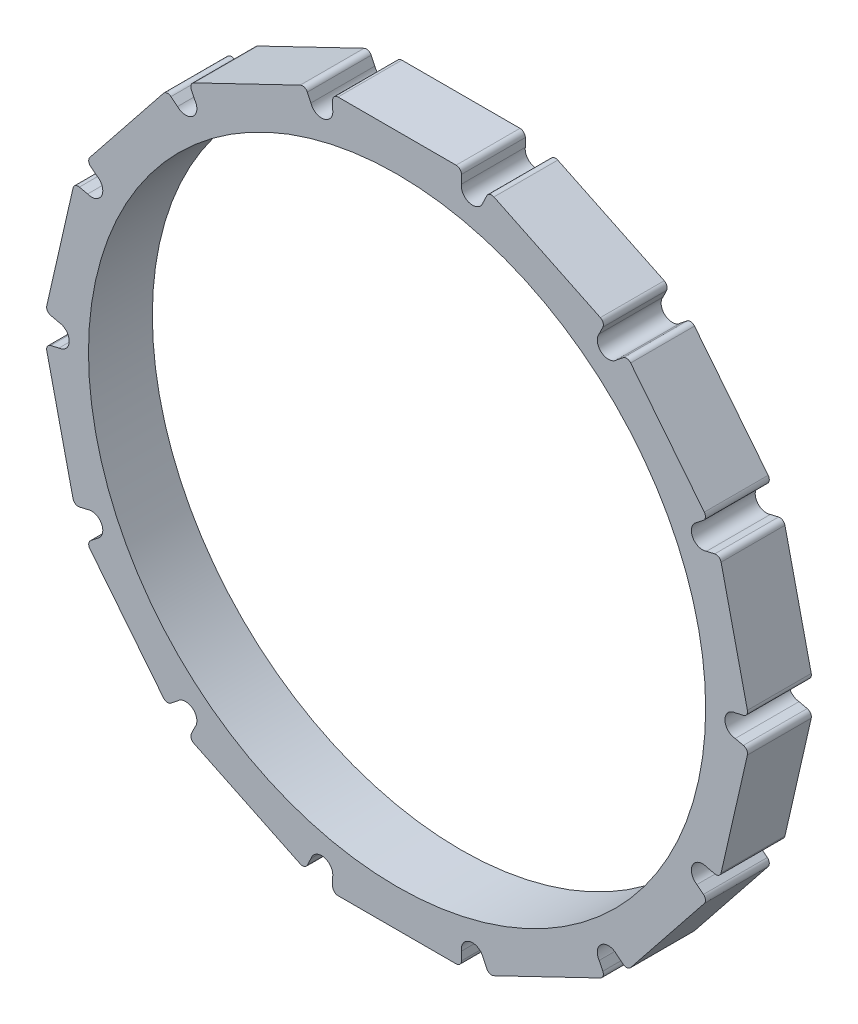
SolidWorks part; units mm, degrees
ref_plane "正面" through (0, 0, 0) normal (0, 0, 1) x (1, 0, 0)
ref_plane "平面" through (0, 0, 0) normal (0, 1, 0) x (1, 0, 0)
ref_plane "右側面" through (0, 0, 0) normal (1, 0, 0) x (0, 0, -1)
sketch "ｽｹｯﾁ1" plane through (0, 0, 0) normal (0, 0, 1) x (1, 0, 0)
  circle A0 centre (0, 0) radius 34.5
  dimension "D1" = 69
extrude "ﾎﾞｽ - 押し出し1" add sketch "ｽｹｯﾁ1" along normal blind 4
sketch "ｽｹｯﾁ2" plane through (0, 0, 4) normal (0, 0, 1) x (1, 0, 0)
  circle A0 centre (0, 0) radius 31.5
  circle A1 centre (0, 0) radius 34.5 construction
  dimension "D1" = 3
extrude "ﾎﾞｽ - 押し出し2" add sketch "ｽｹｯﾁ2" along normal blind 3
sketch "ｽｹｯﾁ3" plane through (0, 0, 4) normal (0, 0, 1) x (1, 0, 0)
  line L1 (-6.05, 30.5) -> (6.05, 30.5)
  line L2 (-6.05, 30.5) -> (-6.05, 32.5)
  line L3 (-6.05, 32.5) -> (6.05, 32.5)
  line L4 (6.05, 30.5) -> (6.05, 32.5)
  line L5 (-6.05, 30.5) -> (6.05, 32.5) construction
  line L6 (-6.05, 32.5) -> (6.05, 30.5) construction
  circle A0 centre (0, 0) radius 31.5 construction
  point P0 (0, 31.5)
  dimension "D1" = 12.1
  dimension "D2" = 1
extrude "ﾎﾞｽ - 押し出し3" add sketch "ｽｹｯﾁ3" along normal blind 3
pattern_circular "円形ﾊﾟﾀｰﾝ1" count 14 over 360 about axis through (0, 0, 0) along (0, 0, 1) of "ﾎﾞｽ - 押し出し3"
sketch "ｽｹｯﾁ5" plane through (0, 0, 7) normal (0, 0, 1) x (1, 0, 0)
  line L0 (-7.0895, 31.0613) -> (0, 0) construction
  circle A0 centre (-7.0895, 31.0613) radius 1.05
  dimension "D1" = 2.1
extrude "ｶｯﾄ - 押し出し1" cut sketch "ｽｹｯﾁ5" against normal blind 3
pattern_circular "円形ﾊﾟﾀｰﾝ2" count 14 over 360 about axis through (0, 0, 0) along (0, 0, 1) of "ｶｯﾄ - 押し出し1"
sketch "ｽｹｯﾁ6" plane through (0, 0, 7) normal (0, 0, 1) x (1, 0, 0)
  circle A0 centre (0, 0) radius 4.5
  dimension "D1" = 9
extrude "ｶｯﾄ - 押し出し2" cut sketch "ｽｹｯﾁ6" against normal through all
sketch "ｽｹｯﾁ7" plane through (0, 0, 7) normal (0, 0, 1) x (1, 0, 0)
  circle A0 centre (0, 0) radius 10.5
  circle A1 centre (0, 0) radius 29
  circle A2 centre (0, 0) radius 4.5 construction
  dimension "D1" = 58
  dimension "D2" = 6
extrude "ｶｯﾄ - 押し出し3" cut sketch "ｽｹｯﾁ7" against normal through all and the other way through all
sketch "ｽｹｯﾁ8" plane through (0, 0, 7) normal (0, 0, 1) x (1, 0, 0)
  line L0 (-10.2329, 2.3534) -> (-4.1739, 28.6981)
  line L1 (0, 29) -> (-4.4863, 9.4933)
  line L2 (0, 0) -> (0, 29) construction
  circle A0 centre (0, 0) radius 10.5 construction
  circle A1 centre (0, 0) radius 29 construction
  arc A2 (0, 29) -> (-4.1739, 28.6981) centre (0, 0) ccw
  arc A3 (-4.4863, 9.4933) -> (-10.2329, 2.3534) centre (0, 0) ccw
  dimension "D1" = 4
extrude "ﾎﾞｽ - 押し出し4" add sketch "ｽｹｯﾁ8" against normal up to surface (7 mm away) up to face at (4.5, 0, 0)
pattern_circular "円形ﾊﾟﾀｰﾝ3" count 6 over 360 about axis through (0, 0, 0) along (0, 0, 1) of "ﾎﾞｽ - 押し出し4"
mirror "ﾐﾗｰ1" about plane through (0, 0, 0) normal (1, 0, 0) of "円形ﾊﾟﾀｰﾝ3", "ﾎﾞｽ - 押し出し4"
fillet "ﾌｨﾚｯﾄ1" radius 0.5 2 edges at (-33.0314, -1.3336, 5.5) (-30.3389, -13.1302, 5.5)
fillet "ﾌｨﾚｯﾄ2" radius 0.5 26 edges at (-8.6504, -31.9065, 5.5) (-6.05, -32.5, 5.5) (6.05, -32.5, 5.5) (8.6504, -31.9065, 5.5) (19.5521, -26.6565, 5.5) (21.6374, -24.9935, 5.5) (29.1816, -15.5333, 5.5) (30.3389, -13.1302, 5.5) (33.0314, -1.3336, 5.5) (33.0314, 1.3336, 5.5) (30.3389, 13.1302, 5.5) (29.1816, 15.5333, 5.5) (21.6374, 24.9935, 5.5) (19.5521, 26.6565, 5.5) (8.6504, 31.9065, 5.5) (6.05, 32.5, 5.5) (-6.05, 32.5, 5.5) (-8.6504, 31.9065, 5.5) (-19.5521, 26.6565, 5.5) (-21.6374, 24.9935, 5.5) (-29.1816, 15.5333, 5.5) (-30.3389, 13.1302, 5.5) (-33.0314, 1.3336, 5.5) (-19.5521, -26.6565, 5.5) (-21.6374, -24.9935, 5.5) (-29.1816, -15.5333, 5.5)
sketch "ｽｹｯﾁ9" plane through (0, 0, 0) normal (0, 0, -1) x (-1, 0, 0)
  circle A0 centre (0, 0) radius 34.5
extrude "ｶｯﾄ - 押し出し4" cut sketch "ｽｹｯﾁ9" against normal blind 4
sketch "ｽｹｯﾁ10" plane through (0, 0, 7) normal (0, 0, 1) x (1, 0, 0)
  circle A0 centre (0, 0) radius 29
extrude "ｶｯﾄ - 押し出し5" cut sketch "ｽｹｯﾁ10" against normal through all
sketch "ｽｹｯﾁ11" plane through (0, 0, 7) normal (0, 0, 1) x (1, 0, 0)
  line L42 (-19.1016, -26.8734) -> (-9.1008, -31.6895)
  line L43 (-8.4334, -31.456) -> (-8.0903, -30.7434)
  line L44 (-6.05, -31.2091) -> (-6.05, -32)
  line L45 (-5.55, -32.5) -> (5.55, -32.5)
  line L46 (6.05, -32) -> (6.05, -31.2091)
  line L47 (8.0903, -30.7434) -> (8.4334, -31.456)
  line L48 (9.1008, -31.6895) -> (19.1016, -26.8734)
  line L49 (19.3351, -26.206) -> (18.992, -25.4935)
  line L50 (20.6282, -24.1887) -> (21.2465, -24.6818)
  line L51 (21.9492, -24.6026) -> (28.8699, -15.9243)
  line L52 (28.7907, -15.2216) -> (28.1724, -14.7285)
  line L53 (29.0804, -12.843) -> (29.8514, -13.019)
  line L54 (30.4502, -12.6428) -> (32.9201, -1.8211)
  line L55 (32.5439, -1.2224) -> (31.7729, -1.0464)
  line L56 (31.7729, 1.0464) -> (32.5439, 1.2224)
  line L57 (32.9201, 1.8211) -> (30.4502, 12.6428)
  line L58 (29.8514, 13.019) -> (29.0804, 12.843)
  line L59 (28.1724, 14.7285) -> (28.7907, 15.2216)
  line L60 (28.8699, 15.9243) -> (21.9492, 24.6026)
  line L61 (21.2465, 24.6818) -> (20.6282, 24.1887)
  line L62 (18.992, 25.4935) -> (19.3351, 26.206)
  line L63 (19.1016, 26.8734) -> (9.1008, 31.6895)
  line L64 (8.4334, 31.456) -> (8.0903, 30.7434)
  line L65 (6.05, 31.2091) -> (6.05, 32)
  line L66 (5.55, 32.5) -> (-5.55, 32.5)
  line L67 (-6.05, 32) -> (-6.05, 31.2091)
  line L68 (-8.0903, 30.7434) -> (-8.4334, 31.456)
  line L69 (-9.1008, 31.6895) -> (-19.1016, 26.8734)
  line L70 (-19.3351, 26.206) -> (-18.992, 25.4935)
  line L71 (-20.6282, 24.1887) -> (-21.2465, 24.6818)
  line L72 (-21.9492, 24.6026) -> (-28.8699, 15.9243)
  line L73 (-28.7907, 15.2216) -> (-28.1724, 14.7285)
  line L74 (-29.0804, 12.843) -> (-29.8514, 13.019)
  line L75 (-30.4502, 12.6428) -> (-32.9201, 1.8211)
  line L76 (-32.5439, 1.2224) -> (-31.7729, 1.0464)
  line L77 (-31.7729, -1.0464) -> (-32.5439, -1.2224)
  line L78 (-32.9201, -1.8211) -> (-30.4502, -12.6428)
  line L79 (-29.8514, -13.019) -> (-29.0804, -12.843)
  line L80 (-28.1724, -14.7285) -> (-28.7907, -15.2216)
  line L81 (-28.8699, -15.9243) -> (-21.9492, -24.6026)
  line L82 (-21.2465, -24.6818) -> (-20.6282, -24.1887)
  line L83 (-18.992, -25.4935) -> (-19.3351, -26.206)
  line L84 (-19.1016, -26.8734) -> (-9.1008, -31.6895)
  line L85 (-8.4334, -31.456) -> (-8.0903, -30.7434)
  line L86 (-6.05, -31.2091) -> (-6.05, -32)
  line L87 (-5.55, -32.5) -> (5.55, -32.5)
  line L88 (6.05, -32) -> (6.05, -31.2091)
  line L89 (8.0903, -30.7434) -> (8.4334, -31.456)
  line L90 (9.1008, -31.6895) -> (19.1016, -26.8734)
  line L91 (19.3351, -26.206) -> (18.992, -25.4935)
  line L92 (20.6282, -24.1887) -> (21.2465, -24.6818)
  line L93 (21.9492, -24.6026) -> (28.8699, -15.9243)
  line L94 (28.7907, -15.2216) -> (28.1724, -14.7285)
  line L95 (29.0804, -12.843) -> (29.8514, -13.019)
  line L96 (30.4502, -12.6428) -> (32.9201, -1.8211)
  line L97 (32.5439, -1.2224) -> (31.7729, -1.0464)
  line L98 (31.7729, 1.0464) -> (32.5439, 1.2224)
  line L99 (32.9201, 1.8211) -> (30.4502, 12.6428)
  line L100 (29.8514, 13.019) -> (29.0804, 12.843)
  line L101 (28.1724, 14.7285) -> (28.7907, 15.2216)
  line L102 (28.8699, 15.9243) -> (21.9492, 24.6026)
  line L103 (21.2465, 24.6818) -> (20.6282, 24.1887)
  line L104 (18.992, 25.4935) -> (19.3351, 26.206)
  line L105 (19.1016, 26.8734) -> (9.1008, 31.6895)
  line L106 (8.4334, 31.456) -> (8.0903, 30.7434)
  line L107 (6.05, 31.2091) -> (6.05, 32)
  line L108 (5.55, 32.5) -> (-5.55, 32.5)
  line L109 (-6.05, 32) -> (-6.05, 31.2091)
  line L110 (-8.0903, 30.7434) -> (-8.4334, 31.456)
  line L111 (-9.1008, 31.6895) -> (-19.1016, 26.8734)
  line L112 (-19.3351, 26.206) -> (-18.992, 25.4935)
  line L113 (-20.6282, 24.1887) -> (-21.2465, 24.6818)
  line L114 (-21.9492, 24.6026) -> (-28.8699, 15.9243)
  line L115 (-28.7907, 15.2216) -> (-28.1724, 14.7285)
  line L116 (-29.0804, 12.843) -> (-29.8514, 13.019)
  line L117 (-30.4502, 12.6428) -> (-32.9201, 1.8211)
  line L118 (-32.5439, 1.2224) -> (-31.7729, 1.0464)
  line L119 (-31.7729, -1.0464) -> (-32.5439, -1.2224)
  line L120 (-32.9201, -1.8211) -> (-30.4502, -12.6428)
  line L121 (-29.8514, -13.019) -> (-29.0804, -12.843)
  line L122 (-28.1724, -14.7285) -> (-28.7907, -15.2216)
  line L123 (-28.8699, -15.9243) -> (-21.9492, -24.6026)
  line L124 (-21.2465, -24.6818) -> (-20.6282, -24.1887)
  line L125 (-18.992, -25.4935) -> (-19.3351, -26.206)
  circle A1 centre (0, 0) radius 29
  circle A2 centre (0, 0) radius 29
  arc A44 (-9.1008, -31.6895) -> (-8.4334, -31.456) centre (-8.8839, -31.2391) ccw
  arc A45 (-6.05, -31.2091) -> (-8.0903, -30.7434) centre (-7.0895, -31.0613) ccw
  arc A46 (-6.05, -32) -> (-5.55, -32.5) centre (-5.55, -32) ccw
  arc A47 (5.55, -32.5) -> (6.05, -32) centre (5.55, -32) ccw
  arc A48 (8.0903, -30.7434) -> (6.05, -31.2091) centre (7.0895, -31.0613) ccw
  arc A49 (8.4334, -31.456) -> (9.1008, -31.6895) centre (8.8839, -31.2391) ccw
  arc A50 (19.1016, -26.8734) -> (19.3351, -26.206) centre (18.8847, -26.4229) ccw
  arc A51 (20.6282, -24.1887) -> (18.992, -25.4935) centre (19.8645, -24.9093) ccw
  arc A52 (21.2465, -24.6818) -> (21.9492, -24.6026) centre (21.5582, -24.2908) ccw
  arc A53 (28.8699, -15.9243) -> (28.7907, -15.2216) centre (28.479, -15.6125) ccw
  arc A54 (29.0804, -12.843) -> (28.1724, -14.7285) centre (28.705, -13.8236) ccw
  arc A55 (29.8514, -13.019) -> (30.4502, -12.6428) centre (29.9627, -12.5315) ccw
  arc A56 (32.9201, -1.8211) -> (32.5439, -1.2224) centre (32.4327, -1.7098) ccw
  arc A57 (31.7729, 1.0464) -> (31.7729, -1.0464) centre (31.8601, 0) ccw
  arc A58 (32.5439, 1.2224) -> (32.9201, 1.8211) centre (32.4327, 1.7098) ccw
  arc A59 (30.4502, 12.6428) -> (29.8514, 13.019) centre (29.9627, 12.5315) ccw
  arc A60 (28.1724, 14.7285) -> (29.0804, 12.843) centre (28.705, 13.8236) ccw
  arc A61 (28.7907, 15.2216) -> (28.8699, 15.9243) centre (28.479, 15.6125) ccw
  arc A62 (21.9492, 24.6026) -> (21.2465, 24.6818) centre (21.5582, 24.2908) ccw
  arc A63 (18.992, 25.4935) -> (20.6282, 24.1887) centre (19.8645, 24.9093) ccw
  arc A64 (19.3351, 26.206) -> (19.1016, 26.8734) centre (18.8847, 26.4229) ccw
  arc A65 (9.1008, 31.6895) -> (8.4334, 31.456) centre (8.8839, 31.2391) ccw
  arc A66 (6.05, 31.2091) -> (8.0903, 30.7434) centre (7.0895, 31.0613) ccw
  arc A67 (6.05, 32) -> (5.55, 32.5) centre (5.55, 32) ccw
  arc A68 (-5.55, 32.5) -> (-6.05, 32) centre (-5.55, 32) ccw
  arc A69 (-8.0903, 30.7434) -> (-6.05, 31.2091) centre (-7.0895, 31.0613) ccw
  arc A70 (-8.4334, 31.456) -> (-9.1008, 31.6895) centre (-8.8839, 31.2391) ccw
  arc A71 (-19.1016, 26.8734) -> (-19.3351, 26.206) centre (-18.8847, 26.4229) ccw
  arc A72 (-20.6282, 24.1887) -> (-18.992, 25.4935) centre (-19.8645, 24.9093) ccw
  arc A73 (-21.2465, 24.6818) -> (-21.9492, 24.6026) centre (-21.5582, 24.2908) ccw
  arc A74 (-28.8699, 15.9243) -> (-28.7907, 15.2216) centre (-28.479, 15.6125) ccw
  arc A75 (-29.0804, 12.843) -> (-28.1724, 14.7285) centre (-28.705, 13.8236) ccw
  arc A76 (-29.8514, 13.019) -> (-30.4502, 12.6428) centre (-29.9627, 12.5315) ccw
  arc A77 (-32.9201, 1.8211) -> (-32.5439, 1.2224) centre (-32.4327, 1.7098) ccw
  arc A78 (-31.7729, -1.0464) -> (-31.7729, 1.0464) centre (-31.8601, 0) ccw
  arc A79 (-32.5439, -1.2224) -> (-32.9201, -1.8211) centre (-32.4327, -1.7098) ccw
  arc A80 (-30.4502, -12.6428) -> (-29.8514, -13.019) centre (-29.9627, -12.5315) ccw
  arc A81 (-28.1724, -14.7285) -> (-29.0804, -12.843) centre (-28.705, -13.8236) ccw
  arc A82 (-28.7907, -15.2216) -> (-28.8699, -15.9243) centre (-28.479, -15.6125) ccw
  arc A83 (-21.9492, -24.6026) -> (-21.2465, -24.6818) centre (-21.5582, -24.2908) ccw
  arc A84 (-18.992, -25.4935) -> (-20.6282, -24.1887) centre (-19.8645, -24.9093) ccw
  arc A85 (-19.3351, -26.206) -> (-19.1016, -26.8734) centre (-18.8847, -26.4229) ccw
  arc A86 (-9.1008, -31.6895) -> (-8.4334, -31.456) centre (-8.8839, -31.2391) ccw
  arc A87 (-6.05, -31.2091) -> (-8.0903, -30.7434) centre (-7.0895, -31.0613) ccw
  arc A88 (-6.05, -32) -> (-5.55, -32.5) centre (-5.55, -32) ccw
  arc A89 (5.55, -32.5) -> (6.05, -32) centre (5.55, -32) ccw
  arc A90 (8.0903, -30.7434) -> (6.05, -31.2091) centre (7.0895, -31.0613) ccw
  arc A91 (8.4334, -31.456) -> (9.1008, -31.6895) centre (8.8839, -31.2391) ccw
  arc A92 (19.1016, -26.8734) -> (19.3351, -26.206) centre (18.8847, -26.4229) ccw
  arc A93 (20.6282, -24.1887) -> (18.992, -25.4935) centre (19.8645, -24.9093) ccw
  arc A94 (21.2465, -24.6818) -> (21.9492, -24.6026) centre (21.5582, -24.2908) ccw
  arc A95 (28.8699, -15.9243) -> (28.7907, -15.2216) centre (28.479, -15.6125) ccw
  arc A96 (29.0804, -12.843) -> (28.1724, -14.7285) centre (28.705, -13.8236) ccw
  arc A97 (29.8514, -13.019) -> (30.4502, -12.6428) centre (29.9627, -12.5315) ccw
  arc A98 (32.9201, -1.8211) -> (32.5439, -1.2224) centre (32.4327, -1.7098) ccw
  arc A99 (31.7729, 1.0464) -> (31.7729, -1.0464) centre (31.8601, 0) ccw
  arc A100 (32.5439, 1.2224) -> (32.9201, 1.8211) centre (32.4327, 1.7098) ccw
  arc A101 (30.4502, 12.6428) -> (29.8514, 13.019) centre (29.9627, 12.5315) ccw
  arc A102 (28.1724, 14.7285) -> (29.0804, 12.843) centre (28.705, 13.8236) ccw
  arc A103 (28.7907, 15.2216) -> (28.8699, 15.9243) centre (28.479, 15.6125) ccw
  arc A104 (21.9492, 24.6026) -> (21.2465, 24.6818) centre (21.5582, 24.2908) ccw
  arc A105 (18.992, 25.4935) -> (20.6282, 24.1887) centre (19.8645, 24.9093) ccw
  arc A106 (19.3351, 26.206) -> (19.1016, 26.8734) centre (18.8847, 26.4229) ccw
  arc A107 (9.1008, 31.6895) -> (8.4334, 31.456) centre (8.8839, 31.2391) ccw
  arc A108 (6.05, 31.2091) -> (8.0903, 30.7434) centre (7.0895, 31.0613) ccw
  arc A109 (6.05, 32) -> (5.55, 32.5) centre (5.55, 32) ccw
  arc A110 (-5.55, 32.5) -> (-6.05, 32) centre (-5.55, 32) ccw
  arc A111 (-8.0903, 30.7434) -> (-6.05, 31.2091) centre (-7.0895, 31.0613) ccw
  arc A112 (-8.4334, 31.456) -> (-9.1008, 31.6895) centre (-8.8839, 31.2391) ccw
  arc A113 (-19.1016, 26.8734) -> (-19.3351, 26.206) centre (-18.8847, 26.4229) ccw
  arc A114 (-20.6282, 24.1887) -> (-18.992, 25.4935) centre (-19.8645, 24.9093) ccw
  arc A115 (-21.2465, 24.6818) -> (-21.9492, 24.6026) centre (-21.5582, 24.2908) ccw
  arc A116 (-28.8699, 15.9243) -> (-28.7907, 15.2216) centre (-28.479, 15.6125) ccw
  arc A117 (-29.0804, 12.843) -> (-28.1724, 14.7285) centre (-28.705, 13.8236) ccw
  arc A118 (-29.8514, 13.019) -> (-30.4502, 12.6428) centre (-29.9627, 12.5315) ccw
  arc A119 (-32.9201, 1.8211) -> (-32.5439, 1.2224) centre (-32.4327, 1.7098) ccw
  arc A120 (-31.7729, -1.0464) -> (-31.7729, 1.0464) centre (-31.8601, 0) ccw
  arc A121 (-32.5439, -1.2224) -> (-32.9201, -1.8211) centre (-32.4327, -1.7098) ccw
  arc A122 (-30.4502, -12.6428) -> (-29.8514, -13.019) centre (-29.9627, -12.5315) ccw
  arc A123 (-28.1724, -14.7285) -> (-29.0804, -12.843) centre (-28.705, -13.8236) ccw
  arc A124 (-28.7907, -15.2216) -> (-28.8699, -15.9243) centre (-28.479, -15.6125) ccw
  arc A125 (-21.9492, -24.6026) -> (-21.2465, -24.6818) centre (-21.5582, -24.2908) ccw
  arc A126 (-18.992, -25.4935) -> (-20.6282, -24.1887) centre (-19.8645, -24.9093) ccw
  arc A127 (-19.3351, -26.206) -> (-19.1016, -26.8734) centre (-18.8847, -26.4229) ccw
  dimension "D1" = 0
  dimension "D2" = 0
extrude "ﾎﾞｽ - 押し出し5" add sketch "ｽｹｯﾁ11" along normal blind 3
